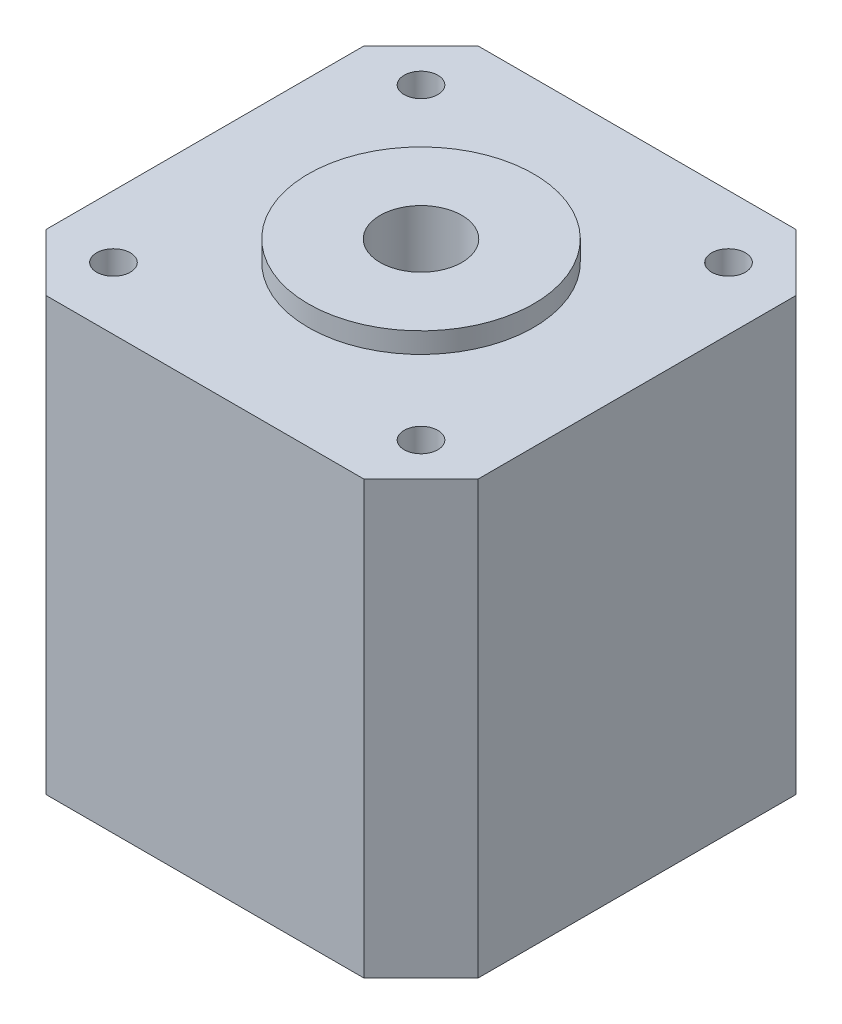
SolidWorks part; units mm, degrees
ref_plane "Plano frontal" through (0, 0, 0) normal (0, 0, 1) x (1, 0, 0)
ref_plane "Plano superior" through (0, 0, 0) normal (0, 1, 0) x (1, 0, 0)
ref_plane "Plano direito" through (0, 0, 0) normal (1, 0, 0) x (0, 0, -1)
sketch "Esboço1" plane through (0, 0, 0) normal (0, 1, 0) x (1, 0, 0)
  line L1 (-21.15, 21.15) -> (21.15, 21.15)
  line L2 (-21.15, 21.15) -> (-21.15, -21.15)
  line L3 (-21.15, -21.15) -> (21.15, -21.15)
  line L4 (21.15, 21.15) -> (21.15, -21.15)
  line L5 (-21.15, 21.15) -> (21.15, -21.15) construction
  line L6 (-21.15, -21.15) -> (21.15, 21.15) construction
  point P0 (0, 0)
  dimension "D1" = 42.3
extrude "Ressalto-extrusão1" add sketch "Esboço1" along normal mid plane 42.3
sketch "Esboço2" plane through (0, 21.15, 0) normal (0, 1, 0) x (1, 0, 0)
  circle A0 centre (0, 0) radius 11.025
  dimension "D1" = 22.05
extrude "Ressalto-extrusão2" add sketch "Esboço2" along normal blind 2
sketch "Esboço3" plane through (0, 23.15, 0) normal (0, 1, 0) x (1, 0, 0)
  circle A0 centre (0, 0) radius 4
  dimension "D1" = 8
chamfer "Chanfro1" distance 5.6 angle 45 3 edges at (-21.15, 0, -21.15) (21.15, 0, -21.15) (21.15, 0, 21.15)
sketch "Esboço4" plane through (0, 21.15, 0) normal (0, 1, 0) x (1, 0, 0)
  line L0 (15.55, 21.15) -> (-15.55, 21.15) construction
  line L1 (-21.15, 15.55) -> (-21.15, -15.55) construction
  line L2 (21.15, -15.55) -> (21.15, 15.55) construction
  line L3 (-15.55, -21.15) -> (15.55, -21.15) construction
  circle A0 centre (-15.05, 15.05) radius 1.65
  circle A1 centre (15.05, 15.05) radius 1.65
  circle A2 centre (15.05, -15.05) radius 1.65
  circle A3 centre (-15.05, -15.05) radius 1.65
  dimension "D1" = 3.3
  dimension "D2" = 6.1
  dimension "D3" = 6.1
  dimension "D4" = 6.1
  dimension "D5" = 6.1
  dimension "D6" = 6.1
  dimension "D7" = 6.1
  dimension "D8" = 6.1
  dimension "D9" = 6.1
extrude "Corte-extrusão1" cut sketch "Esboço4" against normal blind 10
extrude "Corte-extrusão2" cut sketch "Esboço3" against normal blind 70
